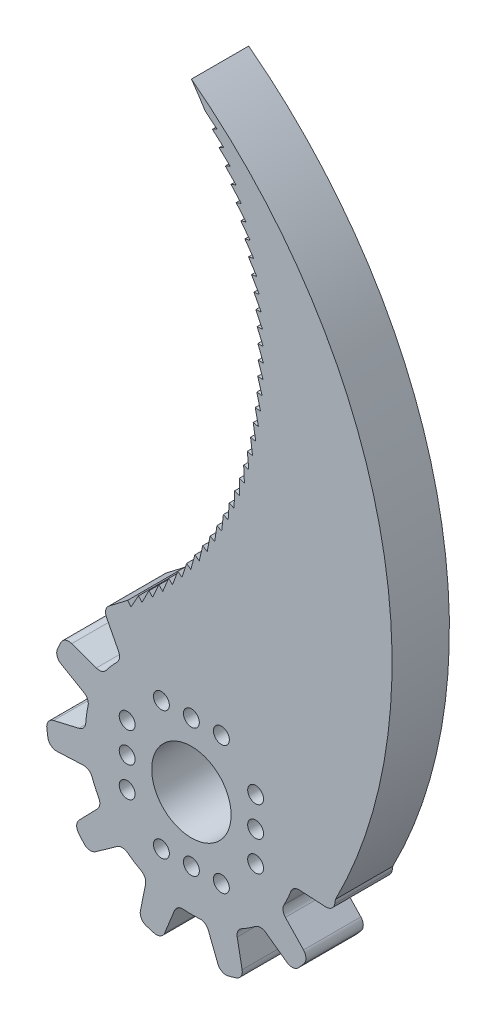
SolidWorks part; units mm, degrees
ref_plane "Plano frontal" through (0, 0, 0) normal (0, 0, 1) x (1, 0, 0)
ref_plane "Plano superior" through (0, 0, 0) normal (0, 1, 0) x (1, 0, 0)
ref_plane "Plano direito" through (0, 0, 0) normal (1, 0, 0) x (0, 0, -1)
sketch "Esboço1" plane through (0, 0, 0) normal (0, 0, 1) x (1, 0, 0)
  line L0 (7.2386, 13.8817) -> (5.3869, 11.5381)
  line L1 (9.6428, 12.3227) -> (8.2635, 9.7019)
  line L2 (13.5945, 7.7645) -> (10.7697, 6.7941)
  line L3 (14.7742, 5.1533) -> (12.1969, 3.6942)
  line L4 (15.6342, -0.8178) -> (12.7332, -0.107)
  line L5 (15.2149, -3.6523) -> (12.2579, -3.4864)
  line L6 (12.7102, -9.1405) -> (10.6541, -6.9741)
  line L7 (10.825, -11.2983) -> (8.4272, -9.5601)
  line L8 (5.7508, -14.5611) -> (5.1923, -11.627)
  line L9 (2.9982, -15.3572) -> (1.9208, -12.5985)
  line L10 (-1.4155, 15.5915) -> (-1.7063, 12.6189)
  line L11 (1.4499, 15.5798) -> (1.7064, 12.6293)
  line L12 (-3.0344, -15.3587) -> (-1.918, -12.5884)
  line L13 (-5.7805, -14.5403) -> (-5.1954, -11.637)
  line L14 (-10.8563, -11.28) -> (-8.4193, -9.5531)
  line L15 (-12.7239, -9.1069) -> (-10.6621, -6.9808)
  line L16 (-15.2313, -3.62) -> (-12.2476, -3.4847)
  line L17 (-15.6276, -0.7821) -> (-12.7436, -0.1083)
  line L18 (-14.7705, 5.1893) -> (-12.1873, 3.69)
  line L19 (-13.5696, 7.7909) -> (-10.7792, 6.7986)
  line L20 (-9.6202, 12.3511) -> (-8.2577, 9.6932)
  line L21 (-7.2034, 13.8904) -> (-5.3924, 11.547)
  arc A0 (-2.4937, 11.738) -> (-4.2472, 11.2232) centre (0, 0) ccw
  circle A1 centre (0, 0) radius 4.5
  arc A2 (0.4829, 16.4928) -> (-0.4474, 16.4938) centre (0, 0) ccw
  arc A3 (1.4499, 15.5798) -> (0.4829, 16.4928) centre (0.4536, 15.4932) ccw
  arc A4 (-1.4155, 15.5915) -> (-0.4474, 16.4938) centre (-0.4203, 15.4941) cw
  arc A5 (9.3229, 13.6135) -> (8.5408, 14.1173) centre (0, 0) ccw
  arc A6 (9.6428, 12.3227) -> (9.3229, 13.6135) centre (8.7579, 12.7885) ccw
  arc A7 (7.2386, 13.8817) -> (8.5408, 14.1173) centre (8.0232, 13.2617) cw
  arc A8 (15.2029, 6.4121) -> (14.8174, 7.2587) centre (0, 0) ccw
  arc A9 (14.7742, 5.1533) -> (15.2029, 6.4121) centre (14.2815, 6.0235) ccw
  arc A10 (13.5945, 7.7645) -> (14.8174, 7.2587) centre (13.9194, 6.8188) cw
  arc A11 (16.2562, -2.8251) -> (16.3896, -1.9045) centre (0, 0) ccw
  arc A12 (15.2149, -3.6523) -> (16.2562, -2.8251) centre (15.2709, -2.6539) ccw
  arc A13 (15.6342, -0.8178) -> (16.3896, -1.9045) centre (15.3962, -1.7891) cw
  arc A14 (12.1482, -11.1654) -> (12.7581, -10.463) centre (0, 0) ccw
  arc A15 (10.825, -11.2983) -> (12.1482, -11.1654) centre (11.4119, -10.4887) ccw
  arc A16 (12.7102, -9.1405) -> (12.7581, -10.463) centre (11.9849, -9.8289) cw
  arc A17 (4.1832, -15.9607) -> (5.0761, -15.6996) centre (0, 0) ccw
  arc A18 (2.9982, -15.3572) -> (4.1832, -15.9607) centre (3.9297, -14.9934) ccw
  arc A19 (5.7508, -14.5611) -> (5.0761, -15.6996) centre (4.7685, -14.7481) cw
  arc A20 (-5.1099, -15.6887) -> (-4.2176, -15.9517) centre (0, 0) ccw
  arc A21 (-5.7805, -14.5403) -> (-5.1099, -15.6887) centre (-4.8002, -14.7378) ccw
  arc A22 (-3.0344, -15.3587) -> (-4.2176, -15.9517) centre (-3.962, -14.9849) cw
  arc A23 (-12.7806, -10.4355) -> (-12.1722, -11.1392) centre (0, 0) ccw
  arc A24 (-12.7239, -9.1069) -> (-12.7806, -10.4355) centre (-12.006, -9.8031) ccw
  arc A25 (-10.8563, -11.28) -> (-12.1722, -11.1392) centre (-11.4345, -10.4641) cw
  arc A26 (-16.3936, -1.8692) -> (-16.2622, -2.7901) centre (0, 0) ccw
  arc A27 (-15.6276, -0.7821) -> (-16.3936, -1.8692) centre (-15.4001, -1.7559) ccw
  arc A28 (-15.2313, -3.62) -> (-16.2622, -2.7901) centre (-15.2766, -2.621) cw
  arc A29 (-14.8018, 7.2906) -> (-15.1891, 6.4448) centre (0, 0) ccw
  arc A30 (-13.5696, 7.7909) -> (-14.8018, 7.2906) centre (-13.9047, 6.8487) ccw
  arc A31 (-14.7705, 5.1893) -> (-15.1891, 6.4448) centre (-14.2685, 6.0542) cw
  arc A32 (-8.5104, 14.1357) -> (-9.2936, 13.6336) centre (0, 0) ccw
  arc A33 (-7.2034, 13.8904) -> (-8.5104, 14.1357) centre (-7.9946, 13.2789) ccw
  arc A34 (-9.6202, 12.3511) -> (-9.2936, 13.6336) centre (-8.7303, 12.8073) cw
  arc A35 (-8.4439, 8.5265) -> (-9.6407, 7.1454) centre (0, 0) ccw
  arc A36 (-11.7132, 2.6078) -> (-11.9734, 0.7989) centre (0, 0) ccw
  arc A37 (-11.2637, -4.1388) -> (-10.5046, -5.8012) centre (0, 0) ccw
  arc A38 (-7.238, -9.5714) -> (-5.7006, -10.5595) centre (0, 0) ccw
  arc A39 (-0.9143, -11.9651) -> (0.9132, -11.9652) centre (0, 0) ccw
  arc A40 (5.6997, -10.56) -> (7.2371, -9.572) centre (0, 0) ccw
  arc A41 (10.504, -5.8022) -> (11.2633, -4.1398) centre (0, 0) ccw
  arc A42 (11.9734, 0.7978) -> (11.7134, 2.6068) centre (0, 0) ccw
  arc A43 (9.6414, 7.1445) -> (8.4447, 8.5257) centre (0, 0) ccw
  arc A44 (4.2482, 11.2229) -> (2.4948, 11.7378) centre (0, 0) ccw
  arc A45 (8.4272, -9.5601) -> (7.2371, -9.572) centre (7.8402, -10.3697) ccw
  arc A46 (5.1923, -11.627) -> (5.6997, -10.56) centre (6.1747, -11.44) cw
  arc A47 (1.9208, -12.5985) -> (0.9132, -11.9652) centre (0.9893, -12.9623) ccw
  arc A48 (-1.918, -12.5884) -> (-0.9143, -11.9651) centre (-0.9905, -12.9622) cw
  arc A49 (-5.1954, -11.637) -> (-5.7006, -10.5595) centre (-6.1757, -11.4395) ccw
  arc A50 (-8.4193, -9.5531) -> (-7.238, -9.5714) centre (-7.8411, -10.369) cw
  arc A51 (-10.6621, -6.9808) -> (-10.5046, -5.8012) centre (-11.3799, -6.2847) ccw
  arc A52 (-12.2476, -3.4847) -> (-11.2637, -4.1388) centre (-12.2023, -4.4837) cw
  arc A53 (-12.7436, -0.1083) -> (-11.9734, 0.7989) centre (-12.9712, 0.8655) ccw
  arc A54 (-12.1873, 3.69) -> (-11.7132, 2.6078) centre (-12.6893, 2.8251) cw
  arc A55 (-10.7792, 6.7986) -> (-9.6407, 7.1454) centre (-10.4441, 7.7408) ccw
  arc A56 (10.6541, -6.9741) -> (10.504, -5.8022) centre (11.3794, -6.2857) cw
  arc A57 (12.2579, -3.4864) -> (11.2633, -4.1398) centre (12.2019, -4.4848) ccw
  arc A58 (12.7332, -0.107) -> (11.9734, 0.7978) centre (12.9712, 0.8643) cw
  arc A59 (12.1969, 3.6942) -> (11.7134, 2.6068) centre (12.6896, 2.824) ccw
  arc A60 (10.7697, 6.7941) -> (9.6414, 7.1445) centre (10.4448, 7.7399) cw
  arc A61 (8.2635, 9.7019) -> (8.4447, 8.5257) centre (9.1484, 9.2362) ccw
  arc A62 (5.3869, 11.5381) -> (4.2482, 11.2229) centre (4.6022, 12.1581) cw
  arc A63 (2.4948, 11.7378) -> (1.7064, 12.6293) centre (2.7026, 12.716) cw
  arc A64 (-2.4937, 11.738) -> (-1.7063, 12.6189) centre (-2.7015, 12.7162) ccw
  arc A65 (-5.3924, 11.547) -> (-4.2472, 11.2232) centre (-4.6012, 12.1585) ccw
  arc A66 (-8.2577, 9.6932) -> (-8.4439, 8.5265) centre (-9.1476, 9.237) cw
  point P94 (0, 0)
  dimension "D1" = 1
  dimension "D2" = 11
  dimension "D3" = 1
extrude "Ressalto-extrusão1" add sketch "Esboço1" along normal blind 6.5
sketch "Esboço3" plane through (0, 0, 0) normal (0, 0, -1) x (-1, 0, 0)
  line L0 (0, 0) -> (0, 7.28) construction
  line L1 (0, 0) -> (7.28, 0) construction
  line L2 (0, 0) -> (0, -7.28) construction
  line L3 (0, 0) -> (-7.28, 0) construction
  circle A0 centre (3.4, 7.28) radius 0.9
  circle A1 centre (0, 7.28) radius 0.9
  circle A2 centre (-3.4, 7.28) radius 0.9
  circle A3 centre (7.28, -3.4) radius 0.9
  circle A4 centre (7.28, 0) radius 0.9
  circle A5 centre (7.28, 3.4) radius 0.9
  circle A6 centre (-3.4, -7.28) radius 0.9
  circle A7 centre (0, -7.28) radius 0.9
  circle A8 centre (3.4, -7.28) radius 0.9
  circle A9 centre (-7.28, 3.4) radius 0.9
  circle A10 centre (-7.28, 0) radius 0.9
  circle A11 centre (-7.28, -3.4) radius 0.9
  point P5 (0, 7.28)
  point P15 (7.28, 0)
  point P22 (0, -7.28)
  point P29 (-7.28, 0)
  point P33 (0, 0)
extrude "Corte-extrusão4" cut sketch "Esboço3" against normal blind 11.8
sketch "Esboço5" plane through (0, 0, 0) normal (0, 0, -1) x (-1, 0, 0)
  line L0 (-7.28, 3.4) -> (-7.28, -3.4) construction
  line L1 (8.18, 3.4) -> (6.38, 3.4)
  line L2 (8.18, 3.4) -> (8.18, -3.4)
  line L3 (8.18, -3.4) -> (6.38, -3.4)
  line L4 (6.38, 3.4) -> (6.38, -3.4)
  line L5 (7.28, -3.4) -> (7.28, 3.4) construction
  line L6 (8.18, 0) -> (6.38, 0) construction
  line L7 (-8.18, 0) -> (-6.38, 0) construction
  line L8 (-8.18, -3.4) -> (-8.18, 3.4)
  line L9 (-8.18, -3.4) -> (-6.38, -3.4)
  line L10 (-6.38, -3.4) -> (-6.38, 3.4)
  line L11 (-8.18, 3.4) -> (-6.38, 3.4)
  circle A0 centre (7.28, -3.4) radius 0.9 construction
  point P0 (7.28, 0)
  point P8 (-7.28, 0)
  point P17 (0, 0)
extrude "Corte-extrusão5" cut sketch "Esboço5" against normal blind 1
sketch "Esboço6" plane through (0, 0, 6.5) normal (0, 0, 1) x (1, 0, 0)
  line L0 (7.2441, 41.3827) -> (7.2425, 41.3703)
  line L1 (-9.2936, 13.6336) -> (-6.1958, 9.0891)
  line L2 (16.3294, -2.3657) -> (10.8863, -1.5772)
  line L3 (2.3813, 66.2608) -> (2.9069, 66.5502)
  line L4 (2.9069, 66.5502) -> (1.5703, 67.6388)
  line L5 (3.1428, 64.8407) -> (3.6796, 65.1088)
  line L6 (3.6796, 65.1088) -> (2.3874, 66.2499)
  line L7 (3.8471, 63.3914) -> (4.3942, 63.6379)
  line L8 (4.3942, 63.6379) -> (3.1485, 64.8296)
  line L9 (4.4931, 61.9151) -> (5.0495, 62.1396)
  line L10 (5.0495, 62.1396) -> (3.8524, 63.38)
  line L11 (5.0796, 60.4142) -> (5.6445, 60.6163)
  line L12 (5.6445, 60.6163) -> (4.4978, 61.9035)
  line L13 (5.6058, 58.8911) -> (6.1784, 59.0705)
  line L14 (6.1784, 59.0705) -> (5.0839, 60.4025)
  line L15 (6.0709, 57.3483) -> (6.6501, 57.5047)
  line L16 (6.6501, 57.5047) -> (5.6097, 58.8792)
  line L17 (6.474, 55.7881) -> (7.0591, 55.9213)
  line L18 (7.0591, 55.9213) -> (6.0743, 57.3362)
  line L19 (6.8146, 54.2131) -> (7.4045, 54.3229)
  line L20 (7.4045, 54.3229) -> (6.4769, 55.7759)
  line L21 (7.0922, 52.6257) -> (7.6859, 52.7119)
  line L22 (7.6859, 52.7119) -> (6.817, 54.2008)
  line L23 (7.3062, 51.0286) -> (7.9029, 51.091)
  line L24 (7.9029, 51.091) -> (7.0941, 52.6134)
  line L25 (7.4563, 49.4242) -> (8.055, 49.4628)
  line L26 (8.055, 49.4628) -> (7.3076, 51.0162)
  line L27 (7.5423, 47.8151) -> (8.1421, 47.8297)
  line L28 (8.1421, 47.8297) -> (7.4572, 49.4117)
  line L29 (7.5641, 46.2038) -> (8.164, 46.1945)
  line L30 (8.164, 46.1945) -> (7.5427, 47.8026)
  line L31 (7.5216, 44.5929) -> (8.1206, 44.5597)
  line L32 (8.1206, 44.5597) -> (7.564, 46.1913)
  line L33 (7.4148, 42.9851) -> (8.0121, 42.928)
  line L34 (8.0121, 42.928) -> (7.521, 44.5804)
  line L35 (7.2441, 41.3827) -> (7.8386, 41.3019)
  line L36 (7.8386, 41.3019) -> (7.4138, 42.9726)
  line L37 (7.0096, 39.7884) -> (7.6004, 39.684)
  line L38 (7.6004, 39.684) -> (7.2425, 41.3703)
  line L39 (6.7116, 38.2048) -> (7.2978, 38.0769)
  line L40 (7.2978, 38.0769) -> (7.0075, 39.7761)
  line L41 (6.3508, 36.6343) -> (6.9314, 36.4831)
  line L42 (6.9314, 36.4831) -> (6.7091, 38.1926)
  line L43 (5.9276, 35.0795) -> (6.5017, 34.9052)
  line L44 (6.5017, 34.9052) -> (6.3477, 36.6222)
  line L45 (5.4427, 33.5427) -> (6.0094, 33.3457)
  line L46 (6.0094, 33.3457) -> (5.9241, 35.0675)
  line L47 (4.8969, 32.0265) -> (5.4554, 31.8071)
  line L48 (5.4554, 31.8071) -> (5.4387, 33.5309)
  line L49 (4.2911, 30.5333) -> (4.8403, 30.2918)
  line L50 (4.8403, 30.2918) -> (4.8925, 32.0149)
  line L51 (3.6262, 29.0655) -> (4.1654, 28.8022)
  line L52 (4.1654, 28.8022) -> (4.2862, 30.5218)
  line L53 (2.9033, 27.6253) -> (3.4316, 27.3407)
  line L54 (3.4316, 27.3407) -> (3.6209, 29.0542)
  line L55 (2.1236, 26.2151) -> (2.64, 25.9097)
  line L56 (2.64, 25.9097) -> (2.8975, 27.6142)
  line L57 (1.2882, 24.8371) -> (1.7921, 24.5114)
  line L58 (1.7921, 24.5114) -> (2.1173, 26.2043)
  line L59 (0.3985, 23.4936) -> (0.889, 23.148)
  line L60 (0.889, 23.148) -> (1.2815, 24.8266)
  line L61 (-0.544, 22.1866) -> (-0.0677, 21.8217)
  line L62 (-0.0677, 21.8217) -> (0.3914, 23.4833)
  line L63 (-1.5379, 20.9182) -> (-1.0766, 20.5346)
  line L64 (-1.0766, 20.5346) -> (-0.5515, 22.1766)
  line L65 (-2.5817, 19.6905) -> (-2.136, 19.2888)
  line L66 (-2.136, 19.2888) -> (-1.5459, 20.9085)
  line L67 (-3.6735, 18.5053) -> (-3.2442, 18.0862)
  line L68 (-3.2442, 18.0862) -> (-2.59, 19.6811)
  line L69 (-4.8118, 17.3647) -> (-4.3995, 16.9288)
  line L70 (-4.3995, 16.9288) -> (-3.6822, 18.4963)
  line L71 (-5.9946, 16.2704) -> (-5.6001, 15.8183)
  line L72 (-5.6001, 15.8183) -> (-4.8208, 17.356)
  line L73 (-7.2202, 15.2241) -> (-6.844, 14.7567)
  line L74 (-6.844, 14.7567) -> (-6.004, 16.2621)
  line L75 (-7.2202, 15.2241) -> (-9.2936, 13.6336)
  line L76 (7.0096, 39.7884) -> (7.0075, 39.7761)
  line L77 (6.7116, 38.2048) -> (6.7091, 38.1926)
  line L78 (6.3477, 36.6222) -> (6.3508, 36.6343)
  line L79 (5.9241, 35.0675) -> (5.9276, 35.0795)
  line L82 (4.8925, 32.0149) -> (4.8969, 32.0265)
  line L83 (4.2862, 30.5218) -> (4.2911, 30.5333)
  line L84 (3.6209, 29.0542) -> (3.6262, 29.0655)
  line L85 (2.9033, 27.6253) -> (2.8975, 27.6142)
  line L86 (2.1173, 26.2043) -> (2.1236, 26.2151)
  line L87 (1.2815, 24.8266) -> (1.2882, 24.8371)
  line L88 (0.3914, 23.4833) -> (0.3985, 23.4936)
  line L89 (-0.544, 22.1866) -> (-0.5515, 22.1766)
  line L90 (-1.5379, 20.9182) -> (-1.5459, 20.9085)
  line L91 (-2.5817, 19.6905) -> (-2.59, 19.6811)
  line L92 (-3.6822, 18.4963) -> (-3.6735, 18.5053)
  line L93 (-4.8208, 17.356) -> (-4.8118, 17.3647)
  line L94 (-6.004, 16.2621) -> (-5.9946, 16.2704)
  line L96 (5.4387, 33.5309) -> (5.4427, 33.5427)
  arc A0 (0, 70) -> (1.5703, 67.6388) centre (-32.831, 46.4637) cw
  arc A1 (7.5641, 46.2038) -> (7.564, 46.1913) centre (-32.831, 46.4637) cw
  arc A2 (0, 70) -> (16.3294, -2.3657) centre (-34.9562, 24.0869) cw
  arc A3 (16.2562, -2.8251) -> (16.3896, -1.9045) centre (0, 0) ccw construction
  circle A4 centre (0, 0) radius 11
  arc A5 (7.5423, 47.8151) -> (7.5427, 47.8026) centre (-32.831, 46.4637) cw
  arc A6 (7.5216, 44.5929) -> (7.521, 44.5804) centre (-32.831, 46.4637) cw
  arc A7 (7.4148, 42.9851) -> (7.4138, 42.9726) centre (-32.831, 46.4637) cw
  arc A8 (7.4563, 49.4242) -> (7.4572, 49.4117) centre (-32.831, 46.4637) cw
  arc A9 (7.3062, 51.0286) -> (7.3076, 51.0162) centre (-32.831, 46.4637) cw
  arc A10 (7.0922, 52.6257) -> (7.0941, 52.6134) centre (-32.831, 46.4637) cw
  arc A11 (6.8146, 54.2131) -> (6.817, 54.2008) centre (-32.831, 46.4637) cw
  arc A12 (6.474, 55.7881) -> (6.4769, 55.7759) centre (-32.831, 46.4637) cw
  arc A13 (6.0709, 57.3483) -> (6.0743, 57.3362) centre (-32.831, 46.4637) cw
  arc A14 (5.6058, 58.8911) -> (5.6097, 58.8792) centre (-32.831, 46.4637) cw
  arc A15 (3.1428, 64.8407) -> (3.1485, 64.8296) centre (-32.831, 46.4637) cw
  arc A16 (2.3813, 66.2608) -> (2.3874, 66.2499) centre (-32.831, 46.4637) cw
  arc A17 (3.8471, 63.3914) -> (3.8524, 63.38) centre (-32.831, 46.4637) cw
  arc A18 (4.4931, 61.9151) -> (4.4978, 61.9035) centre (-32.831, 46.4637) cw
  arc A19 (5.0796, 60.4142) -> (5.0839, 60.4025) centre (-32.831, 46.4637) cw
  point P124 (-32.831, 46.4637)
  dimension "D2" = 36
  dimension "D1" = 70
extrude "Ressalto-extrusão2" add sketch "Esboço6" against normal blind 6.5
